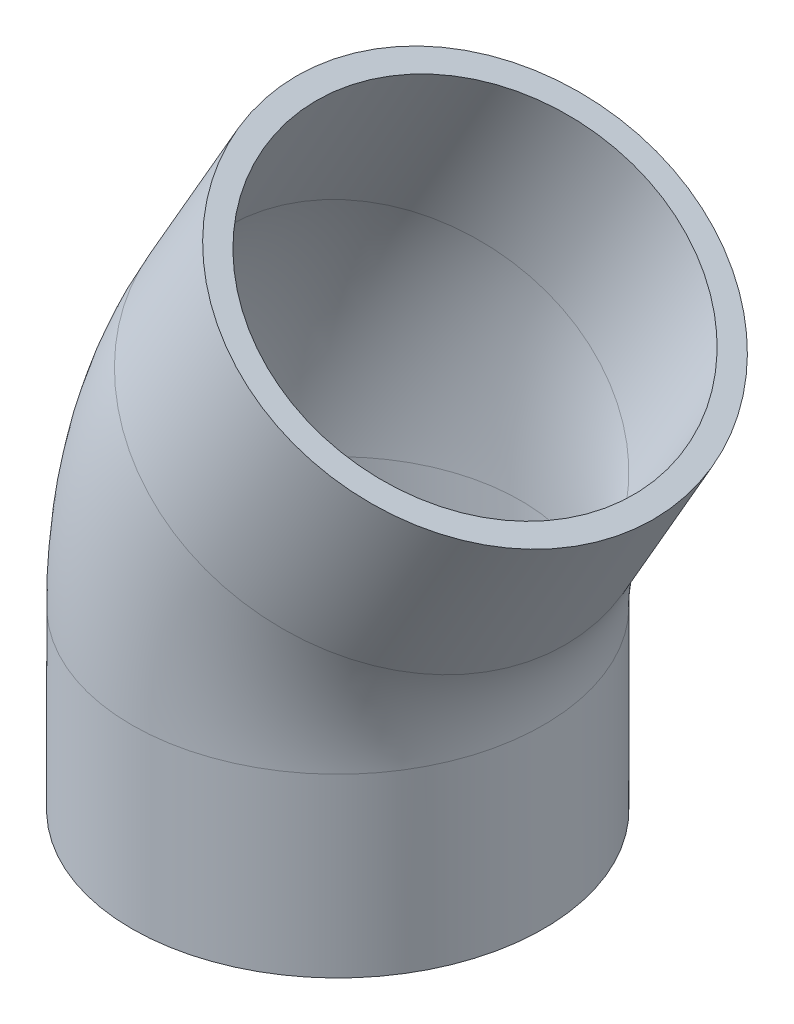
SolidWorks part; units mm, degrees
ref_plane "Front Plane" through (0, 0, 0) normal (0, 0, 1) x (1, 0, 0)
ref_plane "Top Plane" through (0, 0, 0) normal (0, 1, 0) x (1, 0, 0)
ref_plane "Right Plane" through (0, 0, 0) normal (1, 0, 0) x (0, 0, -1)
sketch3d "3DSketch1"
  line L0 (0, 0, 0) -> (0, 19.282, 0)
  line L1 (5.359, 39.282, 0) -> (15, 55.9808, 0)
  arc A0 (0, 19.282, 0) -> (5.359, 39.282, 0) centre (40, 19.282, 0) ccw
  point P6 (0, 30, 0)
  point P8 (40, 19.282, -40)
  dimension "D2" = 30
  dimension "D4" = 40
  dimension "D1" = 150
  dimension "D3" = 30
sketch "Sketch2" plane through (0, 0, 0) normal (0, 1, 0) x (1, 0, 0)
  circle A0 centre (0, 0) radius 20
  dimension "D1" = 40
sweep "Sweep-Thin1" add profiles "Sketch2" path "3DSketch1" parameters "D1"=2.5
